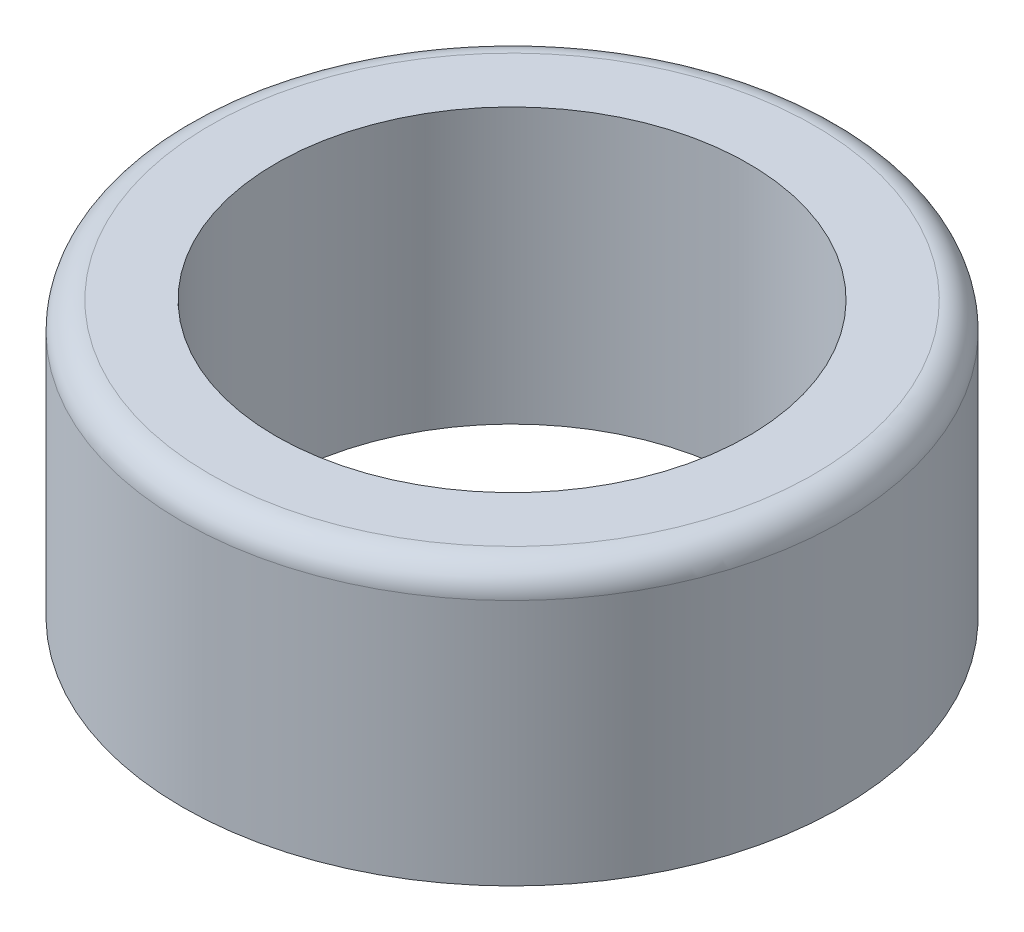
SolidWorks part; units mm, degrees
material "天然橡胶"
ref_plane "前视基准面" through (0, 0, 0) normal (0, 0, 1) x (1, 0, 0)
ref_plane "上视基准面" through (0, 0, 0) normal (0, 1, 0) x (1, 0, 0)
ref_plane "右视基准面" through (0, 0, 0) normal (1, 0, 0) x (0, 0, -1)
sketch "草图1" plane through (0, 0, 0) normal (0, 1, 0) x (1, 0, 0)
  line L0 (0.4731, 8.587) -> (0.4731, 4.3078)
  line L1 (0, -2.7698) -> (0, 1.1) construction
  line L2 (-0.4731, 8.587) -> (-0.4731, 4.3078)
  line L3 (7.2, -4.7032) -> (3.4941, -2.5636)
  line L4 (0, 4.3337) -> (0, 11.8114) construction
  line L5 (7.6731, -3.8837) -> (3.9672, -1.7441)
  line L6 (-7.6731, -3.8837) -> (-3.9672, -1.7441)
  line L7 (-7.2, -4.7032) -> (-3.4941, -2.5636)
  circle A0 centre (0, 0) radius 1.1
  circle A1 centre (0, 0) radius 8.6
  circle A2 centre (0, 0) radius 12
  circle A3 centre (0, 0) radius 3.4997
  circle A4 centre (0, 0) radius 4.3337
  circle A5 centre (0, 0) radius 9.1283
  point P25 (0, 0)
  dimension "D1" = 3
  dimension "D3" = 17.2
  dimension "D2" = 24
extrude "凸台-拉伸1" add sketch "草图1" along normal blind 10
fillet "圆角1" radius 1 1 edges at (0, 10, 12)
